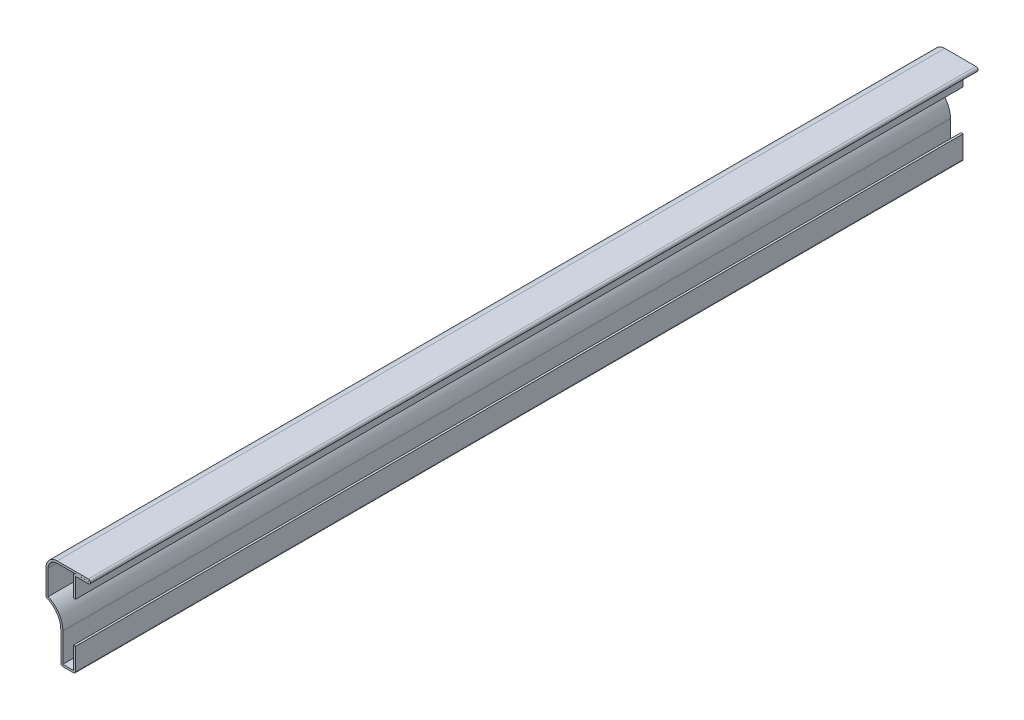
SolidWorks part; units mm, degrees
ref_plane "Front Plane" through (0, 0, 0) normal (0, 0, 1) x (1, 0, 0)
ref_plane "Top Plane" through (0, 0, 0) normal (0, 1, 0) x (1, 0, 0)
ref_plane "Right Plane" through (0, 0, 0) normal (1, 0, 0) x (0, 0, -1)
sketch "Sketch1" plane through (0, 0, 0) normal (0, 0, 1) x (1, 0, 0)
  line L0 (0, 27.7812) -> (0, 36.2966)
  line L1 (0, 36.2966) -> (5.4483, 36.2966)
  line L2 (5.4483, 38.1) -> (-7.9375, 38.1)
  line L3 (-12.7, 33.3375) -> (-12.7, 22.225)
  line L4 (-6.35, 13.2447) -> (-6.35, 0)
  line L5 (-6.35, 0) -> (0, 0)
  line L6 (0, 0) -> (0, 10.3187)
  arc A0 (5.4483, 36.2966) -> (5.4483, 38.1) centre (5.4483, 37.1983) ccw
  arc A1 (-7.9375, 38.1) -> (-12.7, 33.3375) centre (-7.9375, 33.3375) ccw
  arc A2 (-12.7, 22.225) -> (-6.35, 13.2447) centre (-15.875, 13.2447) cw
  point P14 (-6.35, 13.2447)
extrude "Extrude-Thin1" add sketch "Sketch1" against normal blind 381 thin thin type one direction reverse wall 0.889
fillet "Fillet1" radius 0.889 4 edges at (0, 0, -190.5) (-6.35, 0, -190.5) (-0.889, 37.1856, -190.5) (-12.7, 22.225, -190.5)
equation "\"D1@Extrude-Thin1\"=\"D9@Sketch1\"*10"
